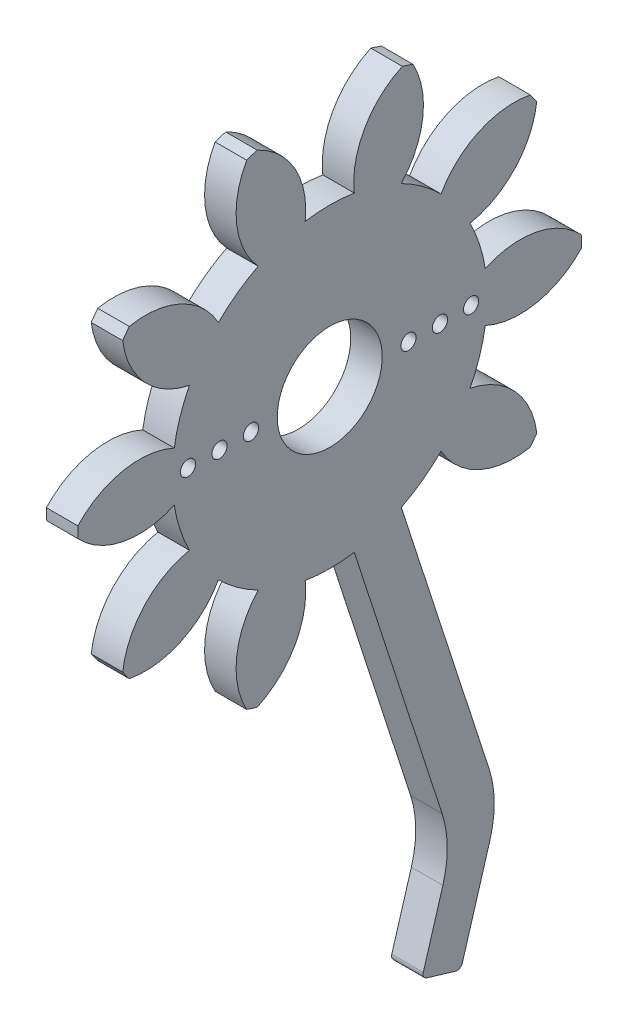
SolidWorks part; units mm, degrees
ref_plane "Plane1" through (0, 0, 0) normal (0, 0, 1) x (1, 0, 0)
ref_plane "Plane2" through (0, 0, 0) normal (0, 1, 0) x (1, 0, 0)
ref_plane "Plane3" through (0, 0, 0) normal (1, 0, 0) x (0, 0, -1)
sketch "HoldingSke" plane through (0, 0, 0) normal (0, 1, 0) x (1, 0, 0)
  line L0 (0, 0) -> (0.2462, -0.0434)
  line L1 (-15, 0) -> (100, 0) construction
  line L2 (0, 0) -> (-2.1039, 2.3779)
  line L3 (0, 0) -> (-11.863, 4.5341)
  line L4 (0, 0) -> (8.5048, 1.4996)
  line L5 (0, 0) -> (-46.8476, -17.4728)
  line L6 (0, 0) -> (-2.4869, -1.6779)
  line L7 (-2.1039, 2.3779) -> (8.6586, 51.2059)
  line L8 (-76.2, 54.61) -> (-74.4, 54.61)
  line L9 (-71.009, 38.7566) -> (-53.1078, 45.2721)
  line L10 (-76.2, 71.12) -> (104.1128, 71.12)
  line L11 (0, 0) -> (-3, 0)
  line L12 (-76.2, 101.6) -> (-76.073, 101.6)
  line L13 (24.9733, 27.94) -> (52.9518, 28.4284)
  line L14 (24.9733, 27.94) -> (24.9743, 27.94)
  line L15 (24.9733, 27.94) -> (100.4006, 29.5858)
  line L16 (-63.627, -4) -> (-12.827, -4)
  circle A0 centre (0, 0) radius 5
  circle A1 centre (0, 0) radius 14.999
  circle A2 centre (0, 0) radius 37.5
  circle A3 centre (0, 0) radius 5
  dimension "MHD" = 29.998
  dimension "Hub_dia" = 75
  dimension "Bore" = 10
  dimension "MBD" = 10
  dimension "Num_teeth" = 10
  dimension "Pitch" = 0.25
  dimension "Overall_len" = 50
  dimension "Show_teeth" = 10
  dimension "Thickness" = 3
  dimension "OAL" = 50.0001
  dimension "T_dim" = 1.8
  dimension "Ap" = 20
  dimension "H" = 19.05
  dimension "Pitch_radius" = 180.3128
  dimension "Width" = 3
  dimension "Backlash" = 0.127
  dimension "Addendum_fac" = 1
  dimension "Dedendum_fac" = 1.25
  dimension "Clearance_fac" = 0.25
  dimension "Dedendum_add" = 0.001
  dimension "Module" = 4
sketch "BasProSke" plane through (0, 0, 0) normal (0, 1, 0) x (1, 0, 0)
  line L0 (-10, 0) -> (60, 0) construction
  line L1 (0, 0) -> (0, 24)
  line L2 (0, 0) -> (3, 0)
  line L3 (3, 0) -> (3, 24)
  line L4 (3, 24) -> (0, 24)
  dimension "Thickness" = 3
  dimension "Diameter" = 48
revolve "Base-Revolve" add sketch "BasProSke" angle 360 about L0
sketch "TooCutSke" plane through (0, 0, 0) normal (1, 0, 0) x (0, 0, -1)
  line L1 (0, 0) -> (0, 107) construction
  line L2 (0, 0) -> (-3.3505, 19.7173) construction
  line L3 (0, 0) -> (-12.2295, 37.6384) construction
  line L4 (-3.3505, 19.7173) -> (-6.1147, 18.8192) construction
  arc A0 (2.338, 14.8157) -> (-2.338, 14.8157) centre (0, 0) ccw
  arc A1 (6.9466, 22.9992) -> (-6.9466, 22.9992) centre (0, 0) ccw
  circle A2 centre (0, 0) radius 20 construction
  circle A3 centre (0, 0) radius 18.7939 construction
  arc A4 (-2.338, 14.8157) -> (-6.9466, 22.9992) centre (-10.2857, 15.7294) ccw
  arc A5 (6.9466, 22.9992) -> (2.338, 14.8157) centre (10.2857, 15.7294) ccw
  dimension "Root_dia" = 29.998
  dimension "Overcut_dia" = 48.0508
  dimension "Pitch_dia" = 40
  dimension "Base_dia" = 37.5877
  dimension "Flank_rad" = 8
  dimension "Half_ang" = 18
  dimension "Half_CT" = 2.9064
extrude "ToothCut" cut sketch "TooCutSke" along normal through all
fillet "Breaks" [suppressed] radius 0.08
fillet "RootFillets" [suppressed] radius 1.001
pattern_circular "TeethCuts" count 10 every 36 about axis through (-10, 0, 0) along (1, 0, 0) of "ToothCut", "RootFillets", "Breaks"
sketch "HubNeaOneSke" plane through (0, 0, 0) normal (-1, 0, 0) x (0, 0, 1)
  circle A0 centre (0, 0) radius 14.999
  dimension "Diameter" = 29.998
extrude "HubNearOne" [suppressed] add sketch "HubNeaOneSke" along normal blind 47.0001
sketch "HubNeaBotSke" plane through (0, 0, 0) normal (-1, 0, 0) x (0, 0, 1)
  circle A0 centre (0, 0) radius 14.999
  dimension "Diameter" = 29.998
extrude "HubNearBoth" [suppressed] add sketch "HubNeaBotSke" along normal blind 23.5
ref_plane "FarPln" through (3, 0, 0) normal (1, 0, 0) x (0, 0, -1)
sketch "HubFarSke" plane through (3, 0, 0) normal (1, 0, 0) x (0, 0, -1)
  circle A0 centre (0, 0) radius 14.999
  dimension "Diameter" = 29.998
extrude "HubFar" [suppressed] add sketch "HubFarSke" along normal blind 23.5
sketch "BorSke" plane through (0, 0, 0) normal (1, 0, 0) x (0, 0, -1)
  circle A0 centre (0, 0) radius 5
  dimension "Diameter" = 10
extrude "Bore" cut sketch "BorSke" along normal mid plane 100.0001
sketch "KeySke" plane through (0, 0, 0) normal (1, 0, 0) x (0, 0, -1)
  line L0 (-2, 0) -> (-2, 6.8)
  line L1 (-2, 6.8) -> (2, 6.8)
  line L2 (2, 6.8) -> (2, 0)
  line L3 (0, 0) -> (0, 34) construction
  line L4 (-2, 0) -> (2, 0)
  dimension "Offset" = 6.8
  dimension "Width" = 4
extrude "Keyway" [suppressed] cut sketch "KeySke" along normal mid plane 100.0001
pattern_circular "Keyway2" [suppressed] count 2 every 90 about axis through (-10, 0, 0) along (1, 0, 0)
sketch "Sketch2" plane through (3, 0, 0) normal (1, 0, 0) x (0, 0, -1)
  line L0 (6.8169, -13.3604) -> (2.338, -14.8157)
  line L1 (2.338, -14.8157) -> (-0.1411, -15.6212)
  line L2 (-0.1411, -15.6212) -> (3.4221, -26.5876)
  line L3 (3.4221, -26.5876) -> (12.2154, -23.7304)
  line L4 (12.2154, -23.7304) -> (8.6522, -12.7641)
  line L5 (8.6522, -12.7641) -> (6.8169, -13.3604)
  arc A0 (-2.338, -14.8157) -> (2.338, -14.8157) centre (0, 0) ccw construction
  dimension "D1" = 9.2459
  dimension "D2" = 11.5307
  dimension "D3" = 4.9614
extrude "Cut-Extrude1" cut sketch "Sketch2" against normal blind 10 contours L3 L4 L5 L0 L1 L2
sketch "Sketch3" plane through (3, 0, 0) normal (1, 0, 0) x (0, 0, -1)
  line L0 (2.338, -14.8157) -> (6.8169, -13.3604)
  line L1 (2.338, -14.8157) -> (11.6663, -43.5252)
  line L2 (11.6663, -43.5252) -> (16.1452, -42.0699)
  line L3 (16.1452, -42.0699) -> (6.8169, -13.3604)
  line L4 (11.6663, -43.5252) -> (8.7656, -53.2412)
  line L5 (12.479, -54.3498) -> (8.7656, -53.2412)
  line L6 (16.1452, -42.0699) -> (12.479, -54.3498)
  line L7 (16.1452, -42.0699) -> (11.6663, -43.5252)
  arc A0 (-2.338, -14.8157) -> (2.338, -14.8157) centre (0, 0) ccw construction
  line M3 (2.338, -14.8157) -> (6.8169, -13.3604)
  dimension "D1" = 45
  dimension "D2" = 3.8754
extrude "Boss-Extrude1" add sketch "Sketch3" against normal blind 3 contours L6 L2 L4 L5 | L2 L3 L1 M3
fillet "Fillet1" radius 10 2 edges at (1.5, -43.5252, -11.6663) (1.5, -42.0699, -16.1452)
fillet "Fillet2" radius 0.5 2 edges at (1.5, -54.3498, -12.479) (1.5, -53.2412, -8.7656)
sketch "Sketch4" plane through (0, 0, 0) normal (-1, 0, 0) x (0, 0, 1)
  circle A0 centre (7.4999, 0.0312) radius 0.7231
  circle A1 centre (10.4999, 0.0436) radius 0.723
  circle A2 centre (13.4999, 0.0561) radius 0.723
  circle A3 centre (-7.4999, -0.0312) radius 0.723
  circle A4 centre (-10.4999, -0.0436) radius 0.723
  circle A5 centre (-13.4626, 0) radius 0.723
  dimension "D1" = 1.4462
  dimension "D2" = 1.446
  dimension "D3" = 1.446
  dimension "D4" = 1.446
  dimension "D5" = 1.446
  dimension "D6" = 1.446
extrude "Cut-Extrude2" cut sketch "Sketch4" against normal through all
equation "' \"Module@HoldingSke\" = 6.35"
equation "' \"Num_teeth@HoldingSke\" = 12"
equation "' \"Ap@HoldingSke\" =  20"
equation "' \"Ap@HoldingSke\" = 20"
equation "' \"Width@HoldingSke\" = 0.5 * 25.4"
equation "' \"Hub_dia@HoldingSke\"= 1 * 25.4"
equation "' \"Hub_dia@HoldingSke\" = 1 * 25.4"
equation "' \"Overall_len@HoldingSke\" = 1.0 * 25.4"
equation "' \"Bore@HoldingSke\" = 0.75 * 25.4"
equation "' \"T_dim@HoldingSke\" = 0.1 * 25.4"
equation "' \"Width@KeySke\" = 0.25 * 25.4"
equation "' \"Show_teeth@HoldingSke\" = 13"
equation "' \"Backlash@HoldingSke\" = 0.009 * 25.4"
equation "' \"Addendum_fac@HoldingSke\" = 1.0"
equation "' \"Dedendum_fac@HoldingSke\" = 1.25"
equation "' \"Dedendum_add@HoldingSke\" = 0.00005 * 25.4"
equation "' \"Clearance_fac@HoldingSke\" = 0.25"
equation "\"Pitch@HoldingSke\" = 1 / \"Module@HoldingSke\""
equation "\"Overcut_dia@TooCutSke\" = (\"Num_teeth@HoldingSke\" + 2 * \"Addendum_fac@HoldingSke\") / \"Pitch@HoldingSke\" + 0.002 * 25.4"
equation "\"Pitch_dia@TooCutSke\" = \"Num_teeth@HoldingSke\" / \"Pitch@HoldingSke\""
equation "\"Base_dia@TooCutSke\" = \"Num_teeth@HoldingSke\" / \"Pitch@HoldingSke\" * cos((\"Ap@HoldingSke\"  * 3.14159265 / 180))"
equation "\"Root_dia@TooCutSke\" = (\"Num_teeth@HoldingSke\" + 2) / \"Pitch@HoldingSke\" - 2 * (\"Addendum_fac@HoldingSke\" + \"Dedendum_fac@HoldingSke\") / \"Pitch@HoldingSke\" - \"Dedendum_add@HoldingSke\" * 2"
equation "\"Half_ang@TooCutSke\" = 180 / \"Num_teeth@HoldingSke\""
equation "\"Half_CT@TooCutSke\" = \"Num_teeth@HoldingSke\" / \"Pitch@HoldingSke\" * sin((3.14159265 / 2 / \"Num_teeth@HoldingSke\")) / 2 - 7 * \"Backlash@HoldingSke\" / 4"
equation "\"Flank_rad@TooCutSke\" = \"Num_teeth@HoldingSke\" / \"Pitch@HoldingSke\" / 5"
equation "\"Radius@RootFillets\" = \"Clearance_fac@HoldingSke\" / \"Pitch@HoldingSke\" + \"Dedendum_add@HoldingSke\""
equation "\"Break_rad@Breaks\" = 0.02 / \"Pitch@HoldingSke\""
equation "\"Thickness@HoldingSke\" = \"Width@HoldingSke\""
equation "\"OAL@HoldingSke\" = \"Thickness@HoldingSke\""
equation "\"MHD@HoldingSke\" = (\"Num_teeth@HoldingSke\" + 2) / \"Pitch@HoldingSke\" - 2 * (\"Addendum_fac@HoldingSke\" + \"Dedendum_fac@HoldingSke\")  / \"Pitch@HoldingSke\" - \"Dedendum_add@HoldingSke\" * 2"
equation "\"MBD@HoldingSke\" = (\"Num_teeth@HoldingSke\" + 2) / \"Pitch@HoldingSke\" - 2 * (\"Addendum_fac@HoldingSke\" + \"Dedendum_fac@HoldingSke\")  / \"Pitch@HoldingSke\" - \"Dedendum_add@HoldingSke\" * 2 - 0.002 * 25.4"
equation "\"MHD@HoldingSke\" = ((sgn( \"MHD@HoldingSke\" - \"Hub_dia@HoldingSke\" )-1)*( \"MHD@HoldingSke\" - \"Hub_dia@HoldingSke\" ))/-2+ \"Hub_dia@HoldingSke\""
equation "\"MBD@HoldingSke\" = ((sgn( \"MBD@HoldingSke\" - \"Bore@HoldingSke\" )-1)*( \"MBD@HoldingSke\" - \"Bore@HoldingSke\" ))/-2+ \"Bore@HoldingSke\""
equation "\"OAL@HoldingSke\" = ((sgn( \"OAL@HoldingSke\" - \"Overall_len@HoldingSke\" )+1)*( \"OAL@HoldingSke\" - \"Overall_len@HoldingSke\" ))/2 + \"Overall_len@HoldingSke\" + 0.000002 * 25.4"
equation "\"Num_teeth@TeethCuts\" = int( \"Show_teeth@HoldingSke\" ) + 1"
equation "\"Num_teeth@TeethCuts\" = ((sgn( \"Num_teeth@TeethCuts\" - \"Num_teeth@HoldingSke\" )-1)*( \"Num_teeth@TeethCuts\" - \"Num_teeth@HoldingSke\" ))/-2+ \"Num_teeth@HoldingSke\""
equation "\"Num_teeth@TeethCuts\" = ((sgn( \"Num_teeth@TeethCuts\" - 2.0)+1)*( \"Num_teeth@TeethCuts\" - 2.0))/2 +2.0"
equation "\"Angle@TeethCuts\" = 360.0 / \"Num_teeth@HoldingSke\""
equation "\"Diameter@BasProSke\" = (\"Num_teeth@HoldingSke\" + 2 * \"Addendum_fac@HoldingSke\") / \"Pitch@HoldingSke\""
equation "\"Thickness@BasProSke\"  = \"Thickness@HoldingSke\""
equation "' \"Fillet_rad@BasProSke\" =  \"Thickness@HoldingSke\" * 0.05"
equation "' \"Fillet_rad@BasProSke\" = \"Thickness@HoldingSke\" * 0.05"
equation "\"MHD@HoldingSke\" = ((sgn( \"MHD@HoldingSke\" - \"Root_dia@TooCutSke\" )-1)*( \"MHD@HoldingSke\" - \"Root_dia@TooCutSke\" ))/-2+ \"Root_dia@TooCutSke\""
equation "\"Diameter@HubNeaOneSke\" = \"MHD@HoldingSke\""
equation "\"Length@HubNearOne\" = \"OAL@HoldingSke\" - \"Thickness@BasProSke\""
equation "\"Diameter@HubNeaBotSke\" = \"MHD@HoldingSke\""
equation "\"Length@HubNearBoth\" = ( \"OAL@HoldingSke\" - \"Thickness@BasProSke\" ) / 2.0"
equation "\"Thickness@FarPln\" = \"Thickness@BasProSke\""
equation "\"Diameter@HubFarSke\" = \"MHD@HoldingSke\""
equation "\"Length@HubFar\" = ( \"OAL@HoldingSke\" - \"Thickness@BasProSke\" ) / 2.0"
equation "\"Diameter@BorSke\" = \"MBD@HoldingSke\""
equation "\"D1@Bore\" = \"OAL@HoldingSke\" * 2.0"
equation "\"D1@Keyway\" = \"OAL@HoldingSke\" * 2.0"
equation "\"Offset@KeySke\" = \"T_dim@HoldingSke\" + \"MBD@HoldingSke\" / 2.0"
